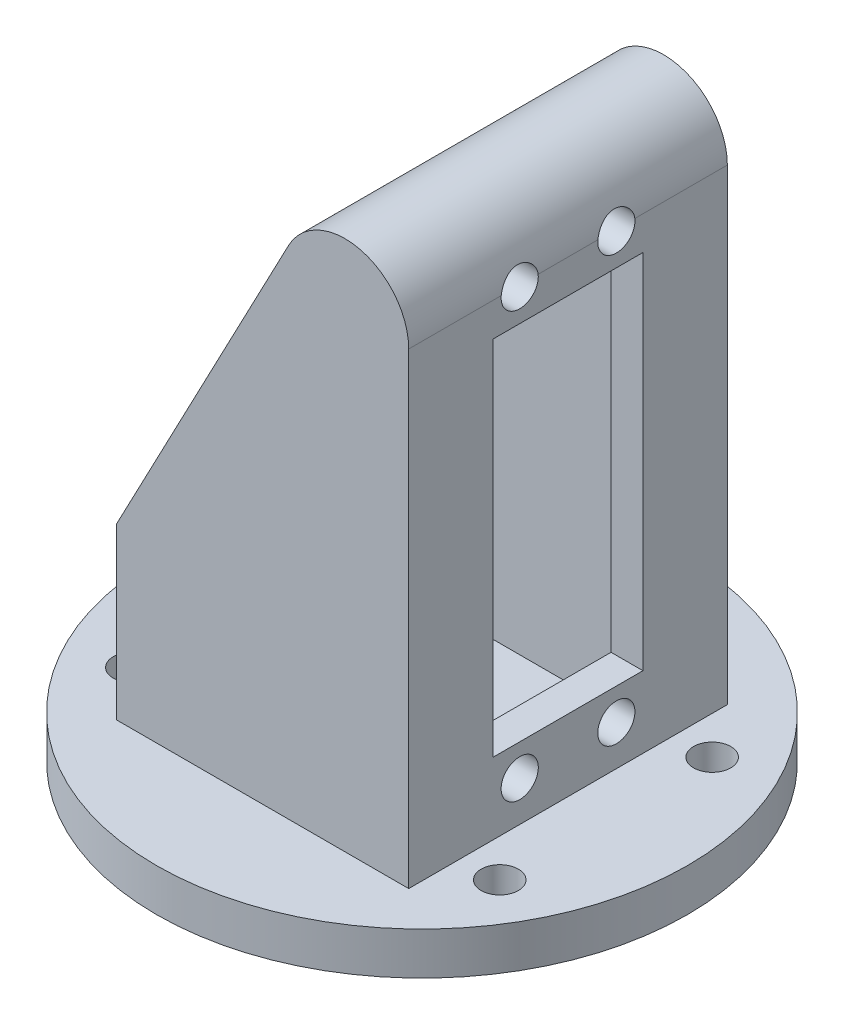
SolidWorks part; units mm, degrees
material "ABS"
ref_plane "Front Plane" through (0, 0, 0) normal (0, 0, 1) x (1, 0, 0)
ref_plane "Top Plane" through (0, 0, 0) normal (0, 1, 0) x (1, 0, 0)
ref_plane "Right Plane" through (0, 0, 0) normal (1, 0, 0) x (0, 0, -1)
sketch "Sketch1" plane through (0, 0, 0) normal (0, 1, 0) x (1, 0, 0)
  line L0 (25, 0) -> (-25, 0) construction
  line L1 (0, 0) -> (0, 25) construction
  line L2 (0, 0) -> (-17.3205, 10) construction
  line L3 (0, 0) -> (17.3205, 10) construction
  line L4 (0, 0) -> (17.3205, -10) construction
  line L5 (0, 0) -> (-17.3205, -10) construction
  circle A0 centre (0, 0) radius 25
  circle A3 centre (-17.3205, 10) radius 1.75
  circle A4 centre (17.3205, 10) radius 1.75
  circle A5 centre (17.3205, -10) radius 1.75
  circle A6 centre (-17.3205, -10) radius 1.75
  point P7 (0, 0)
  dimension "D1" = 50
  dimension "D3" = 20
  dimension "D4" = 3.5
  dimension "D2" = 60
extrude "Boss-Extrude1" add sketch "Sketch1" along normal blind 4
sketch "Sketch2" plane through (0, 4, 0) normal (0, 1, 0) x (1, 0, 0)
  line L1 (13.75, -15) -> (-13.75, -15)
  line L2 (13.75, -15) -> (13.75, 15)
  line L3 (13.75, 15) -> (-13.75, 15)
  line L4 (-13.75, -15) -> (-13.75, 15)
  line L5 (13.75, -15) -> (-13.75, 15) construction
  line L6 (13.75, 15) -> (-13.75, -15) construction
  point P0 (0, 0)
  dimension "D1" = 27.5
  dimension "D2" = 30
extrude "Boss-Extrude2" add sketch "Sketch2" along normal blind 50
sketch "Sketch3" plane through (0, 0, 15) normal (0, 0, 1) x (1, 0, 0)
  line L0 (13.75, 54) -> (13.75, 48)
  line L1 (-13.75, 20) -> (-13.75, 54)
  line L2 (-13.75, 54) -> (13.75, 54)
  line L3 (-13.75, 54) -> (-13.75, 4) construction
  line L4 (-13.75, 20) -> (2.4393, 50.7922)
  line L5 (13.75, 54) -> (13.75, 48)
  line L6 (-13.75, 54) -> (13.75, 54) construction
  line L7 (-13.75, 4) -> (13.75, 4) construction
  arc A0 (2.4393, 50.7922) -> (13.75, 48) centre (7.75, 48) cw
  line M4 (13.75, 4) -> (13.75, 54)
  line M5 (13.75, 54) -> (-13.75, 54)
  line M6 (-13.75, 54) -> (-13.75, 4)
  dimension "D1" = 6
  dimension "D2" = 16
extrude "Cut-Extrude1" cut sketch "Sketch3" against normal through all contours L4 A0 L2 M6 | A0 M5 M4
sketch "Sketch4" plane through (-13.75, 0, 0) normal (-1, 0, 0) x (0, 0, 1)
  line L1 (-8.5, 4.7922) -> (8.5, 4.7922)
  line L2 (-8.5, 4.7922) -> (-8.5, 50.7922)
  line L3 (-8.5, 50.7922) -> (8.5, 50.7922)
  line L4 (8.5, 4.7922) -> (8.5, 50.7922)
  line L5 (-15, 50.7922) -> (15, 50.7922) construction
  line L6 (0, 0) -> (0, 54) construction
  line L7 (15, 54) -> (-15, 54) construction
  dimension "D1" = 17
  dimension "D2" = 46
extrude "Cut-Extrude2" cut sketch "Sketch4" against normal blind 24.5
sketch "Sketch5" plane through (10.75, 0, 0) normal (-1, 0, 0) x (0, 0, 1)
  line L0 (0, 50.7922) -> (0, 4.7922) construction
  line L1 (8.5, 50.7922) -> (-8.5, 50.7922) construction
  line L2 (-8.5, 4.7922) -> (8.5, 4.7922) construction
  line L3 (0, 27.7922) -> (-8.5, 27.7922) construction
  line L4 (-8.5, 50.7922) -> (-8.5, 4.7922) construction
  line L6 (7.05, 10.7422) -> (-7.05, 10.7422)
  line L7 (7.05, 10.7422) -> (7.05, 44.8422)
  line L8 (7.05, 44.8422) -> (-7.05, 44.8422)
  line L9 (-7.05, 10.7422) -> (-7.05, 44.8422)
  line L10 (7.05, 10.7422) -> (-7.05, 44.8422) construction
  line L11 (7.05, 44.8422) -> (-7.05, 10.7422) construction
  circle A0 centre (-4.55, 47.8022) radius 1.75
  circle A4 centre (-4.55, 7.7822) radius 1.75
  circle A5 centre (4.55, 7.7822) radius 1.75
  circle A6 centre (4.55, 47.8022) radius 1.75
  dimension "D4" = 3.5
  dimension "D5" = 34.1
  dimension "D1" = 20.01
  dimension "D2" = 4.55
  dimension "D3" = 14.1
extrude "Cut-Extrude3" cut sketch "Sketch5" against normal up to next
